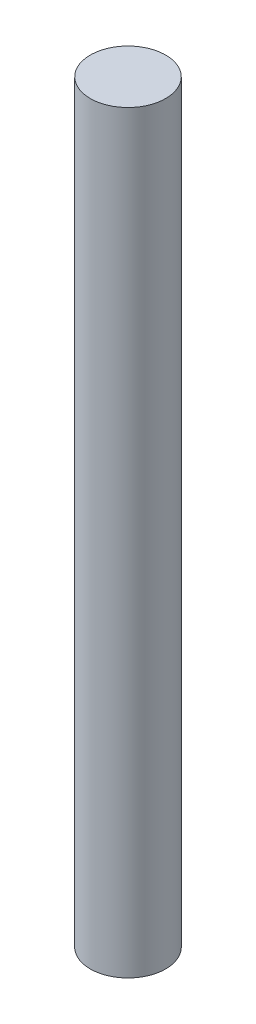
SolidWorks part; units mm, degrees
ref_plane "Front" through (0, 0, 0) normal (0, 0, 1) x (1, 0, 0)
ref_plane "Top" through (0, 0, 0) normal (0, 1, 0) x (1, 0, 0)
ref_plane "Right" through (0, 0, 0) normal (1, 0, 0) x (0, 0, -1)
sketch "草图1" plane through (0, 0, 0) normal (0, 1, 0) x (1, 0, 0)
  circle A0 centre (0, 0) radius 4
  dimension "D1" = 8
extrude "凸台-拉伸1" add sketch "草图1" along normal blind 80
